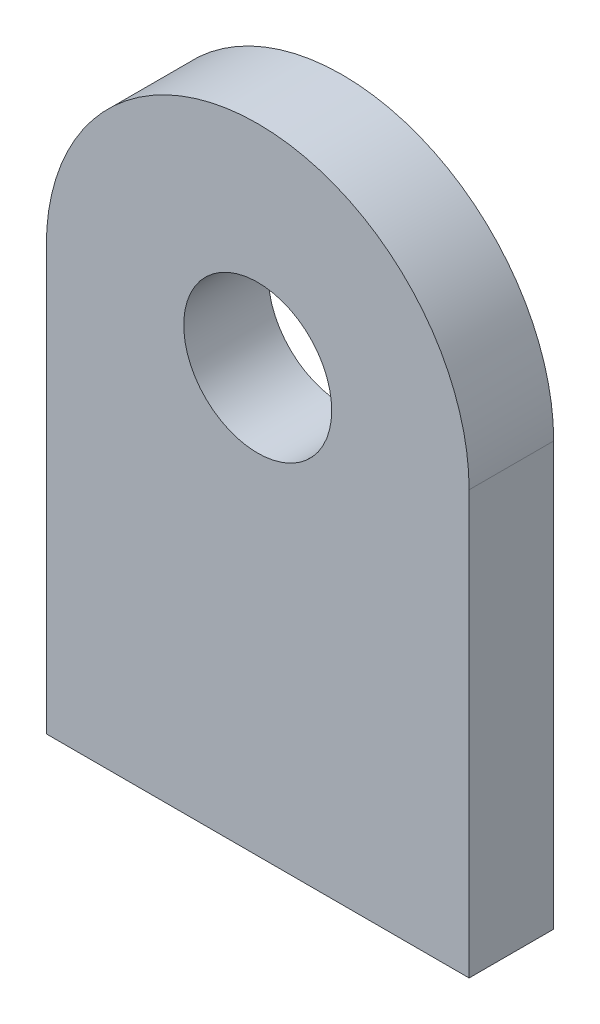
SolidWorks part; units mm, degrees
material "S235J0"
ref_plane "Front Plane" through (0, 0, 0) normal (0, 0, 1) x (1, 0, 0)
ref_plane "Top Plane" through (0, 0, 0) normal (0, 1, 0) x (1, 0, 0)
ref_plane "Right Plane" through (0, 0, 0) normal (1, 0, 0) x (0, 0, -1)
sketch "Sketch1" plane through (0, 0, 0) normal (0, 0, 1) x (1, 0, 0)
  line L0 (-50, 100) -> (-50, 0)
  line L1 (-50, 0) -> (50, 0)
  line L2 (50, 0) -> (50, 100)
  circle A0 centre (0, 100) radius 17.5
  arc A1 (50, 100) -> (-50, 100) centre (0, 100) ccw
  point P2 (127.6404, 0)
  point P5 (0, 0)
  dimension "D1" = 100
  dimension "D2" = 100
  dimension "D3" = 35
extrude "Boss-Extrude1" add sketch "Sketch1" along normal blind 20
